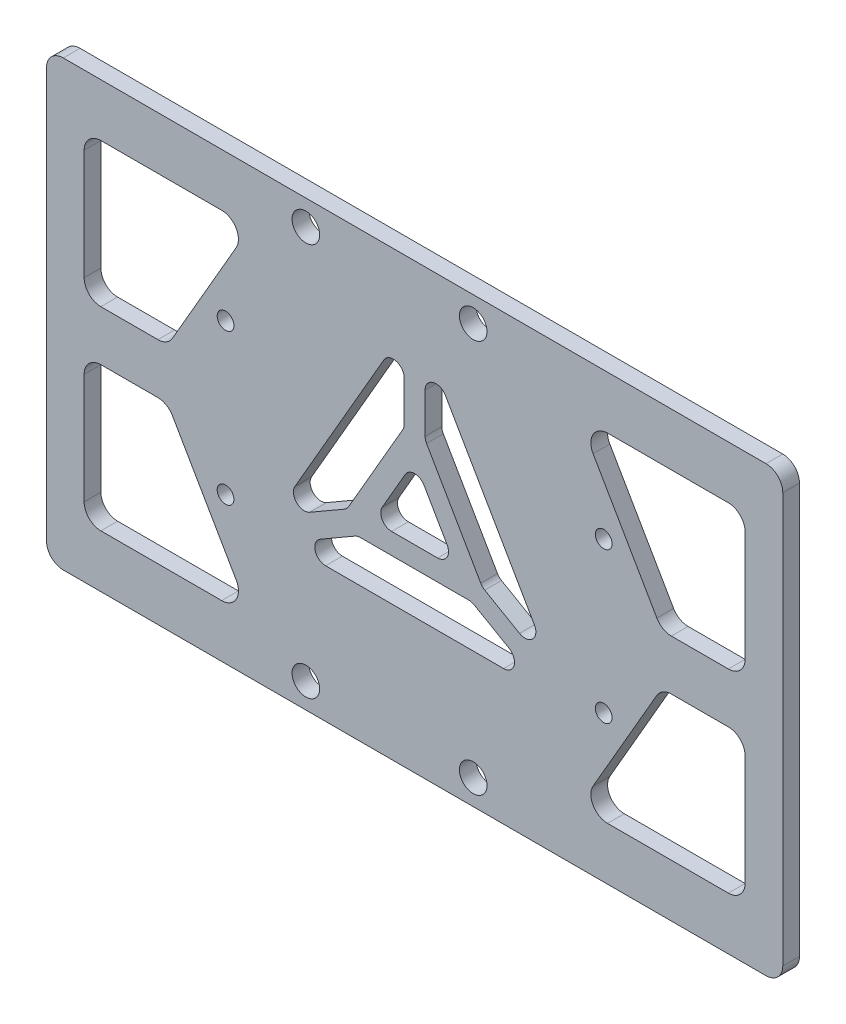
SolidWorks part; units mm, degrees
material "Thornel Mat VMA"
ref_plane "前视基准面" through (0, 0, 0) normal (0, 0, 1) x (1, 0, 0)
ref_plane "上视基准面" through (0, 0, 0) normal (0, 1, 0) x (1, 0, 0)
ref_plane "右视基准面" through (0, 0, 0) normal (1, 0, 0) x (0, 0, -1)
sketch "草图1" plane through (0, 0, 0) normal (0, 0, 1) x (1, 0, 0)
  line L1 (-44, -26.5) -> (44, -26.5)
  line L2 (-44, -26.5) -> (-44, 26.5)
  line L3 (-44, 26.5) -> (44, 26.5)
  line L4 (44, -26.5) -> (44, 26.5)
  line L5 (-44, -26.5) -> (44, 26.5) construction
  line L6 (-44, 26.5) -> (44, -26.5) construction
  point P0 (0, 0)
  dimension "D1" = 53
  dimension "D2" = 88
extrude "凸台-拉伸1" add sketch "草图1" along normal blind 2
sketch "草图2" plane through (0, 0, 2) normal (0, 0, 1) x (1, 0, 0)
  line L0 (-13, 23.5) -> (0, 23.5) construction
  line L1 (0, 23.5) -> (0, 0) construction
  line L2 (0, 0) -> (0, -23.5) construction
  line L3 (0, -23.5) -> (7, -23.5) construction
  line L4 (0, -23.5) -> (-13, -23.5) construction
  line L5 (0, 23.5) -> (7, 23.5) construction
  circle A4 centre (22.6, 9) radius 1 construction
  circle A5 centre (22.6, -9) radius 1 construction
  circle A6 centre (-22.6, -9) radius 1 construction
  circle A7 centre (-22.6, 9) radius 1 construction
  circle A8 centre (7, -23.5) radius 1.65
  circle A9 centre (-13, -23.5) radius 1.65
  circle A10 centre (-13, 23.5) radius 1.65
  circle A11 centre (7, 23.5) radius 1.65
  circle A12 centre (22.6, 9) radius 1
  circle A13 centre (22.6, -9) radius 1
  circle A14 centre (-22.6, -9) radius 1
  circle A15 centre (-22.6, 9) radius 1
  dimension "D7" = 3.3
  dimension "D1" = 23.5
  dimension "D2" = 13
  dimension "D3" = 7
  dimension "D4" = 23.5
  dimension "D5" = 13
  dimension "D6" = 7
extrude "切除-拉伸1" cut sketch "草图2" against normal blind 10
sketch "草图3" plane through (0, 0, 2) normal (0, 0, 1) x (1, 0, 0)
  line L0 (0, 5.7735) -> (-5, -2.8868)
  line L1 (-5, -2.8868) -> (5, -2.8868)
  line L2 (5, -2.8868) -> (0, 5.7735)
  line L3 (0, 0) -> (0, 5.7735) construction
  line L4 (0, 0) -> (-5, -2.8868) construction
  line L5 (0, 0) -> (5, -2.8868) construction
  line L6 (0, 5.7735) -> (0, 24.813) construction
  line L7 (-5, -2.8868) -> (-38.4319, -22.1887) construction
  line L8 (5, -2.8868) -> (41.7087, -24.0806) construction
  line L9 (1.25, 8.6084) -> (1.25, 18.6084)
  line L10 (1.25, 18.6084) -> (16.7404, -8.2217)
  line L11 (16.7404, -8.2217) -> (8.0801, -3.2217)
  line L12 (8.0801, -3.2217) -> (1.25, 8.6084)
  line L13 (-6.8301, -5.3868) -> (6.8301, -5.3868)
  line L14 (6.8301, -5.3868) -> (15.4904, -10.3868)
  line L15 (15.4904, -10.3868) -> (-15.4904, -10.3868)
  line L16 (-15.4904, -10.3868) -> (-6.8301, -5.3868)
  line L17 (-1.25, 8.6084) -> (-8.0801, -3.2217)
  line L18 (-8.0801, -3.2217) -> (-16.7404, -8.2217)
  line L19 (-16.7404, -8.2217) -> (-1.25, 18.6084)
  line L20 (-1.25, 18.6084) -> (-1.25, 8.6084)
  line L21 (0, 0) -> (1.25, 8.6084) construction
  line L22 (0, 0) -> (6.8301, -5.3868) construction
  line L23 (-19.8205, -12.8868) -> (19.8205, -12.8868) construction
  line L24 (19.8205, -12.8868) -> (30.409, -19) construction
  line L25 (30.409, -19) -> (-30.409, -19) construction
  line L26 (-30.409, -19) -> (-19.8205, -12.8868) construction
  line L30 (-20.1, -8.0407) -> (-3.7952, 20.2) construction
  line L31 (-3.7952, 20.2) -> (-9.5687, 20.2) construction
  line L32 (-9.5687, 20.2) -> (-20.1, 1.9593) construction
  line L33 (-20.1, 1.9593) -> (-20.1, -8.0407) construction
  line L34 (20.1, 1.9593) -> (20.1, -8.0407) construction
  line L35 (9.5687, 20.2) -> (20.1, 1.9593) construction
  line L36 (3.7952, 20.2) -> (9.5687, 20.2) construction
  line L37 (20.1, -8.0407) -> (3.7952, 20.2) construction
  circle A0 centre (-13, -23.5) radius 1.65 construction
  circle A3 centre (-13, 23.5) radius 1.65 construction
  circle A4 centre (-22.6, -9) radius 1 construction
  dimension "D11" = 3.3
  dimension "D1" = 120
  dimension "D2" = 10
  dimension "D3" = 1.25
  dimension "D4" = 1.25
  dimension "D5" = 2.5
  dimension "D6" = 5
  dimension "D8" = 120
  dimension "D9" = 2.5
  dimension "D10" = 4.5
  dimension "D12" = 3
  dimension "D13" = 2.5
  dimension "D14" = 5
  dimension "D7" = 3
extrude "切除-拉伸2" cut sketch "草图3" against normal blind 10
fillet "圆角1" radius 1.3 15 edges at (-5, -2.8868, 1) (0, 5.7735, 1) (5, -2.8868, 1) (1.25, 8.6084, 1) (1.25, 18.6084, 1) (16.7404, -8.2217, 1) (8.0801, -3.2217, 1) (-16.7404, -8.2217, 1) (-1.25, 18.6084, 1) (-1.25, 8.6084, 1) (-8.0801, -3.2217, 1) (15.4904, -10.3868, 1) (-15.4904, -10.3868, 1) (-6.8301, -5.3868, 1) (6.8301, -5.3868, 1)
fillet "圆角4" radius 2 4 edges at (44, -26.5, 1) (44, 26.5, 1) (-44, -26.5, 1) (-44, 26.5, 1)
sketch "草图7" plane through (0, 0, 2) normal (0, 0, 1) x (1, 0, 0)
  line L5 (44, -24.5) -> (44, 24.5) construction
  line L6 (19.5978, 20.2) -> (39.5, 20.2)
  line L7 (39.5, 20.2) -> (39.5, 3)
  line L8 (39.5, 3) -> (29.5282, 3)
  line L9 (29.5282, 3) -> (19.5978, 20.2)
  line L10 (0, 0) -> (58.8052, 0) construction
  line L11 (14.3145, -4.02) -> (3.6758, 14.4068) construction
  line L12 (29.5282, -3) -> (19.5978, -20.2)
  line L13 (39.5, -3) -> (29.5282, -3)
  line L14 (39.5, -20.2) -> (39.5, -3)
  line L15 (19.5978, -20.2) -> (39.5, -20.2)
  line L16 (0, 0) -> (0, 45.3359) construction
  line L17 (-39.5, -3) -> (-29.5282, -3)
  line L18 (-39.5, -20.2) -> (-39.5, -3)
  line L19 (-19.5978, -20.2) -> (-39.5, -20.2)
  line L20 (-29.5282, -3) -> (-19.5978, -20.2)
  line L21 (-39.5, 3) -> (-29.5282, 3)
  line L22 (-39.5, 20.2) -> (-39.5, 3)
  line L23 (-19.5978, 20.2) -> (-39.5, 20.2)
  line L24 (-29.5282, 3) -> (-19.5978, 20.2)
  circle A0 centre (7, 23.5) radius 1.65 construction
  circle A1 centre (22.6, 9) radius 1 construction
  dimension "D1" = 3.3
  dimension "D2" = 3
  dimension "D3" = 3
  dimension "D4" = 4.5
extrude "切除-拉伸6" cut sketch "草图7" against normal blind 10
fillet "圆角5" radius 2 16 edges at (19.5978, 20.2, 1) (39.5, 20.2, 1) (39.5, 3, 1) (29.5282, 3, 1) (-39.5, -3, 1) (-29.5282, -3, 1) (-19.5978, -20.2, 1) (-39.5, -20.2, 1) (39.5, -3, 1) (29.5282, -3, 1) (-39.5, 20.2, 1) (-19.5978, 20.2, 1) (-29.5282, 3, 1) (-39.5, 3, 1) (19.5978, -20.2, 1) (39.5, -20.2, 1)
